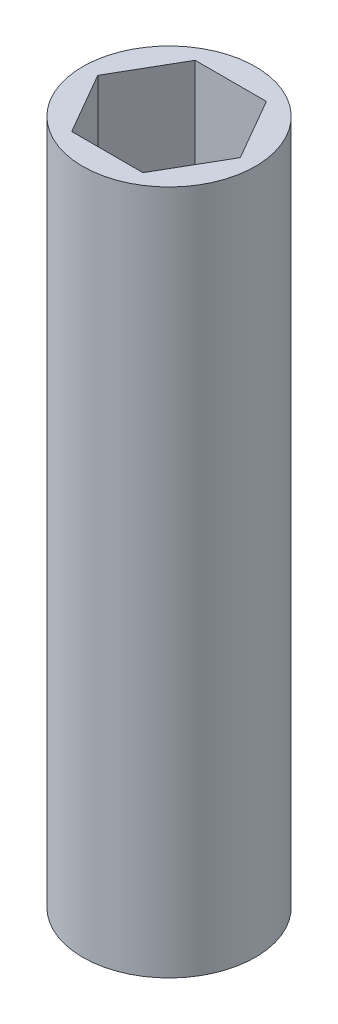
SolidWorks part; units mm, degrees
ref_plane "Front Plane" through (0, 0, 0) normal (0, 0, 1) x (1, 0, 0)
ref_plane "Top Plane" through (0, 0, 0) normal (0, 1, 0) x (1, 0, 0)
ref_plane "Right Plane" through (0, 0, 0) normal (1, 0, 0) x (0, 0, -1)
sketch "Sketch1" plane through (0, 0, 0) normal (0, 1, 0) x (1, 0, 0)
  line L1 (2.9329, -5.08) -> (5.8659, 0)
  line L2 (5.8659, 0) -> (2.9329, 5.08)
  line L3 (2.9329, 5.08) -> (-2.9329, 5.08)
  line L4 (-2.9329, 5.08) -> (-5.8659, 0)
  line L5 (-5.8659, 0) -> (-2.9329, -5.08)
  line L6 (-2.9329, -5.08) -> (2.9329, -5.08)
  circle A0 centre (0, 0) radius 7.112
  circle A1 centre (0, 0) radius 5.08 construction
  dimension "D1" = 10.16
  dimension "D2" = 14.224
extrude "Boss-Extrude1" add sketch "Sketch1" along normal blind 56.388
